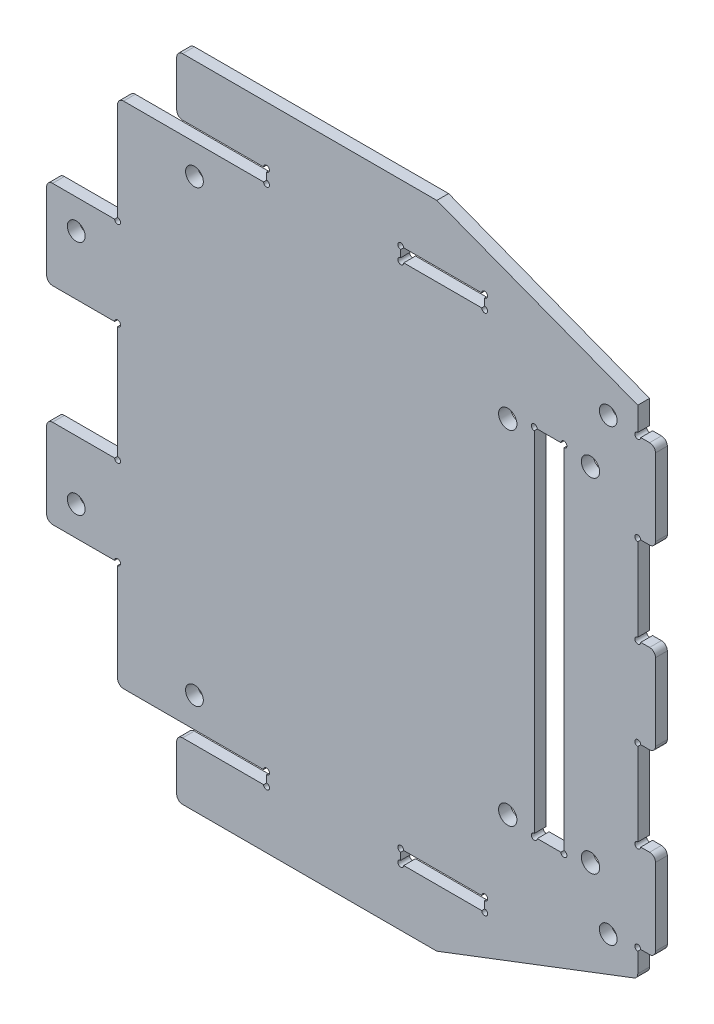
SolidWorks part; units mm, degrees
material "环氧板3240"
ref_plane "前视基准面" through (0, 0, 0) normal (0, 0, 1) x (1, 0, 0)
ref_plane "上视基准面" through (0, 0, 0) normal (0, 1, 0) x (1, 0, 0)
ref_plane "右视基准面" through (0, 0, 0) normal (1, 0, 0) x (0, 0, -1)
other "Configuration Table"
sketch "草图1" plane through (0, 0, 0) normal (0, 0, 1) x (1, 0, 0)
  line L0 (0, 0) -> (0, 55) construction
  line L1 (44, 55) -> (-44, 55)
  line L2 (44, 55) -> (44, -55)
  line L3 (44, -55) -> (-44, -55)
  line L4 (-44, 55) -> (-44, -55)
  line L5 (44, 55) -> (-44, -55) construction
  line L6 (44, -55) -> (-44, 55) construction
  line L7 (18.1, 45.25) -> (3.9, 45.25)
  line L8 (18.1, 45.25) -> (18.1, 43.05)
  line L9 (18.1, 43.05) -> (3.9, 43.05)
  line L10 (3.9, 45.25) -> (3.9, 43.05)
  line L11 (18.1, 45.25) -> (3.9, 43.05) construction
  line L12 (18.1, 43.05) -> (3.9, 45.25) construction
  line L17 (-18.8, -45.25) -> (-44, -45.25)
  line L18 (-18.8, 43.05) -> (-44, 43.05)
  line L23 (-18.8, 43.05) -> (-18.8, 45.25)
  line L24 (-18.8, 45.25) -> (-44, 45.25)
  line L25 (-44, 43.05) -> (-44, 45.25)
  line L26 (-18.8, 43.05) -> (-44, 45.25) construction
  line L27 (105.2978, 0) -> (-44, 0) construction
  line L36 (18.1, -43.05) -> (3.9, -43.05)
  line L37 (3.9, -45.25) -> (3.9, -43.05)
  line L38 (18.1, -45.25) -> (3.9, -45.25)
  line L39 (18.1, -45.25) -> (18.1, -43.05)
  line L40 (47, 22.5) -> (47, 7.5) construction
  line L41 (44, 7.5) -> (47, 7.5)
  line L42 (44, 7.5) -> (44, -7.5)
  line L43 (44, -7.5) -> (47, -7.5)
  line L44 (47, 7.5) -> (47, -7.5)
  line L45 (44, 7.5) -> (47, -7.5) construction
  line L46 (44, -7.5) -> (47, 7.5) construction
  line L47 (44, 37.5) -> (47, 37.5)
  line L48 (44, 37.5) -> (44, 22.5)
  line L49 (44, 22.5) -> (47, 22.5)
  line L50 (47, 37.5) -> (47, 22.5)
  line L51 (44, 37.5) -> (47, 22.5) construction
  line L52 (44, 22.5) -> (47, 37.5) construction
  line L53 (44, -22.5) -> (47, -22.5)
  line L54 (44, -22.5) -> (44, -37.5)
  line L55 (44, -37.5) -> (47, -37.5)
  line L56 (47, -22.5) -> (47, -37.5)
  line L57 (44, -22.5) -> (47, -37.5) construction
  line L58 (44, -37.5) -> (47, -22.5) construction
  line L59 (47, -7.5) -> (47, -22.5) construction
  line L72 (-18.8, 45.25) -> (-44, 43.05) construction
  line L73 (25, 10) -> (15, 10) construction
  line L74 (25, 10) -> (25, -10) construction
  line L75 (25, -10) -> (15, -10) construction
  line L76 (15, 10) -> (15, -10) construction
  line L77 (25, 10) -> (15, -10) construction
  line L78 (25, -10) -> (15, 10) construction
  line L83 (-44, -43.05) -> (-44, -45.25)
  line L84 (-18.8, -43.05) -> (-44, -43.05)
  line L89 (-18.8, -43.05) -> (-18.8, -45.25)
  line L91 (-44, -25) -> (-56, -25)
  line L92 (-44, -25) -> (-44, -10)
  line L93 (-44, -10) -> (-56, -10)
  line L94 (-56, -25) -> (-56, -10)
  line L95 (-44, -25) -> (-56, -10) construction
  line L96 (-44, -10) -> (-56, -25) construction
  line L97 (-44, 10) -> (-56, 10)
  line L98 (-44, 10) -> (-44, 25)
  line L99 (-44, 25) -> (-56, 25)
  line L100 (-56, 10) -> (-56, 25)
  line L101 (-44, 10) -> (-56, 25) construction
  line L102 (-44, 25) -> (-56, 10) construction
  line L104 (10, 55) -> (44, 42)
  line L105 (10, -55) -> (44, -42)
  line L106 (-44, -38) -> (44, -38) construction
  line L107 (-51, 25) -> (-51, 10) construction
  line L108 (-44, -50) -> (-39, -50) construction
  circle A0 centre (-31, -38) radius 1.5
  circle A1 centre (39, -38) radius 1.5
  circle A2 centre (39, 38) radius 1.5
  circle A3 centre (-31, 38) radius 1.5
  circle A4 centre (-51, 20) radius 1.5
  circle A5 centre (-51, -20) radius 1.5
  circle A6 centre (-39, -50) radius 1.5
  circle A7 centre (-39, 50) radius 1.5
  point P4 (0, 0)
  point P11 (11, 44.15)
  point P19 (-50, -17.5)
  point P28 (-31.4, 44.15)
  point P41 (45.5, 0)
  point P45 (45.5, 30)
  point P50 (45.5, -30)
  point P51 (-50, 17.5)
  point P63 (20, 0)
  dimension "D20" = 3
  dimension "D22" = 13
  dimension "D23" = 70
  dimension "D24" = 5
  dimension "D26" = 3
  dimension "D2" = 25.2
  dimension "D3" = 88
  dimension "D4" = 110
  dimension "D5" = 86.1
  dimension "D6" = 2.2
  dimension "D7" = 14.2
  dimension "D8" = 15
  dimension "D9" = 3
  dimension "D10" = 15
  dimension "D11" = 20
  dimension "D12" = 10
  dimension "D13" = 15
  dimension "D14" = 12
  dimension "D15" = 15
  dimension "D16" = 20
  dimension "D17" = 42.4
  dimension "D18" = 13
  dimension "D19" = 34
  dimension "D21" = 17
  dimension "D25" = 5
  dimension "D27" = 5
  dimension "D28" = 5
extrude "凸台-拉伸1" add sketch "草图1" along normal blind 2
sketch "草图2" plane through (0, 0, 2) normal (0, 0, 1) x (1, 0, 0)
  line L0 (-44, 0) -> (47, 0) construction
  line L1 (-44, 10) -> (-44, -10) construction
  line L2 (47, 7.5) -> (47, -7.5) construction
  line L3 (-44, -25) -> (-56, -25) construction
  circle A0 centre (-18.8, -45.25) radius 0.5
  circle A1 centre (-18.8, -43.05) radius 0.5
  circle A2 centre (3.9, -45.25) radius 0.5
  circle A3 centre (3.9, -43.05) radius 0.5
  circle A4 centre (18.1, -43.05) radius 0.5
  circle A5 centre (18.1, -45.25) radius 0.5
  circle A7 centre (18.1, 45.25) radius 0.5
  circle A8 centre (18.1, 43.05) radius 0.5
  circle A9 centre (3.9, 43.05) radius 0.5
  circle A10 centre (3.9, 45.25) radius 0.5
  circle A11 centre (-18.8, 43.05) radius 0.5
  circle A12 centre (-18.8, 45.25) radius 0.5
  circle A13 centre (-44, -25) radius 0.5
  circle A14 centre (-44, -10) radius 0.5
  circle A15 centre (-44, 10) radius 0.5
  circle A16 centre (-44, 25) radius 0.5
  circle A17 centre (44, -37.5) radius 0.5
  circle A18 centre (44, -22.5) radius 0.5
  circle A19 centre (44, -7.5) radius 0.5
  circle A20 centre (44, 22.5) radius 0.5
  circle A21 centre (44, 37.5) radius 0.5
  circle A22 centre (44, 7.5) radius 0.5
  dimension "D1" = 1
extrude "切除-拉伸1" cut sketch "草图2" against normal through all
fillet "圆角1" radius 1 17 edges at (-44, -55, 1) (-44, -45.25, 1) (-44, -43.05, 1) (-56, -25, 1) (-56, -10, 1) (-56, 10, 1) (-56, 25, 1) (-44, 43.05, 1) (-44, 45.25, 1) (-44, 55, 1) (47, 37.5, 1) (47, 22.5, 1) (47, 7.5, 1) (47, -7.5, 1) (47, -22.5, 1) (47, -37.5, 1) (44, -42, 1)
sketch "草图3" plane through (0, 0, 0) normal (0, 0, -1) x (-1, 0, 0)
  line L0 (-47, 0) -> (44, 0) construction
  line L1 (-31.5, 30) -> (-26.5, 30)
  line L2 (-31.5, 30) -> (-31.5, -30)
  line L3 (-31.5, -30) -> (-26.5, -30)
  line L4 (-26.5, 30) -> (-26.5, -30)
  line L5 (-47, 6.5) -> (-47, -6.5) construction
  line L6 (44, 9.5) -> (44, -9.5) construction
  line L7 (-36, 29) -> (-22, 29) construction
  line L8 (-29, 30) -> (-29, -30) construction
  circle A0 centre (-36, 29) radius 1.55
  circle A1 centre (-36, -29) radius 1.55
  circle A2 centre (-22, 29) radius 1.55
  circle A3 centre (-22, -29) radius 1.55
  dimension "D4" = 3.1
  dimension "D5" = 58
  dimension "D1" = 5
  dimension "D2" = 60
  dimension "D3" = 70.5
  dimension "D6" = 14
extrude "切除-拉伸2" cut sketch "草图3" against normal through all
sketch "草图4" plane through (0, 0, 0) normal (0, 0, -1) x (-1, 0, 0)
  line L0 (-31.5, -30) -> (-26.5, -30) construction
  line L1 (-26.5, -30) -> (-26.5, 30) construction
  circle A0 centre (-31.5, 30) radius 0.5
  circle A1 centre (-26.5, 30) radius 0.5
  circle A2 centre (-31.5, -30) radius 0.5
  circle A3 centre (-26.5, -30) radius 0.5
  dimension "D1" = 1
extrude "切除-拉伸3" cut sketch "草图4" against normal through all
sketch "草图5" plane through (0, 0, 2) normal (0, 0, 1) x (1, 0, 0)
  line L0 (10, 55) -> (-43, 55) construction
  line L1 (-44, 55) -> (-34, 55)
  line L2 (-44, 55) -> (-44, 45.25)
  line L3 (-44, 45.25) -> (-34, 45.25)
  line L4 (-34, 55) -> (-34, 45.25)
  line L5 (-19.3, 45.25) -> (-43, 45.25) construction
  line L6 (-44, 54) -> (-44, 46.25) construction
  line L7 (-44, 0) -> (0, 0) construction
  line L8 (-44, 9.5) -> (-44, -9.5) construction
  line L9 (-44, -45.25) -> (-34, -45.25)
  line L10 (-34, -55) -> (-34, -45.25)
  line L11 (-44, -55) -> (-34, -55)
  line L12 (-44, -55) -> (-44, -45.25)
  dimension "D1" = 10
extrude "切除-拉伸4" cut sketch "草图5" against normal blind 10
fillet "圆角2" radius 1 4 edges at (-34, -55, 1) (-34, -45.25, 1) (-34, 45.25, 1) (-34, 55, 1)
